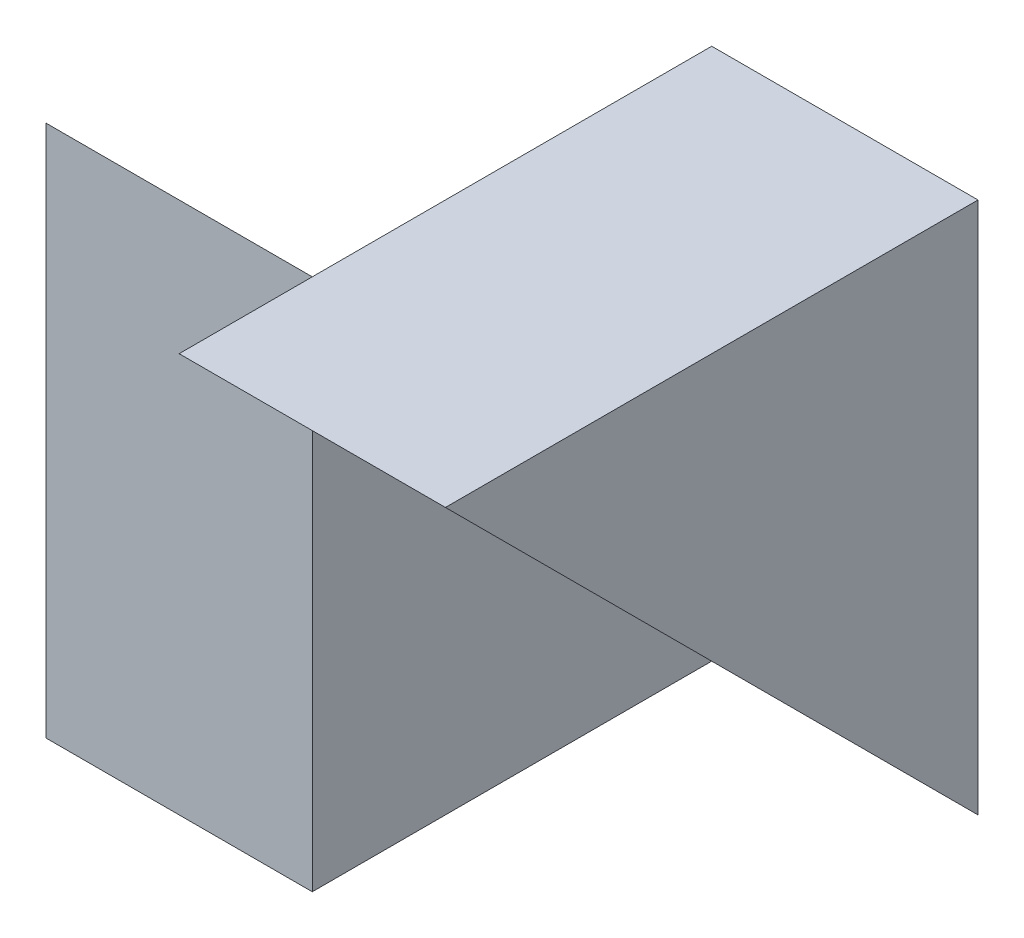
SolidWorks part; units mm, degrees
ref_plane "Front Plane" through (0, 0, 0) normal (0, 0, 1) x (1, 0, 0)
ref_plane "Top Plane" through (0, 0, 0) normal (0, 1, 0) x (1, 0, 0)
ref_plane "Right Plane" through (0, 0, 0) normal (1, 0, 0) x (0, 0, -1)
sketch "Sketch1" plane through (0, 0, 0) normal (1, 0, 0) x (0, 0, -1)
  line L1 (0, 0) -> (4, 0)
  line L2 (0, 0) -> (0, 4)
  line L3 (0, 4) -> (4, 4)
  line L4 (4, 0) -> (4, 4)
  dimension "D1" = 4
  dimension "D2" = 4
extrude "Boss-Extrude1" add sketch "Sketch1" along normal blind 2
sketch "Sketch2" plane through (0, 0, 0) normal (-1, 0, 0) x (0, 0, 1)
  line L0 (-1, 0) -> (-1, 4)
  line L1 (0, 0) -> (-4, 0) construction
  line L2 (-4, 0) -> (-4, 4) construction
  line L3 (-4, 4) -> (-4, 0)
  line L4 (-4, 0) -> (-1, 0)
  line L5 (-4, 4) -> (0, 4) construction
  line L6 (-1, 4) -> (-4, 4)
  dimension "D1" = 3
  dimension "D2" = 4
extrude "Boss-Extrude2" add sketch "Sketch2" along normal blind 2
sketch "Sketch3" plane through (-2, 0, 0) normal (-1, 0, 0) x (0, 0, 1)
  line L0 (-1, 4) -> (-4, 0)
  line L1 (-4, 0) -> (-4, 4)
  line L2 (-4, 4) -> (-1, 4)
extrude "Cut-Extrude1" cut sketch "Sketch3" against normal blind 2
sketch "Sketch4" plane through (2, 0, 0) normal (1, 0, 0) x (0, 0, -1)
  line L0 (4, 0) -> (0, 4)
  line L1 (0, 4) -> (4, 4)
  line L2 (4, 4) -> (4, 0)
  line M4 (0, 4) -> (0, 0)
  line M5 (0, 0) -> (4, 0)
extrude "Cut-Extrude2" cut sketch "Sketch4" against normal blind 2 contours L0 M5 M4
